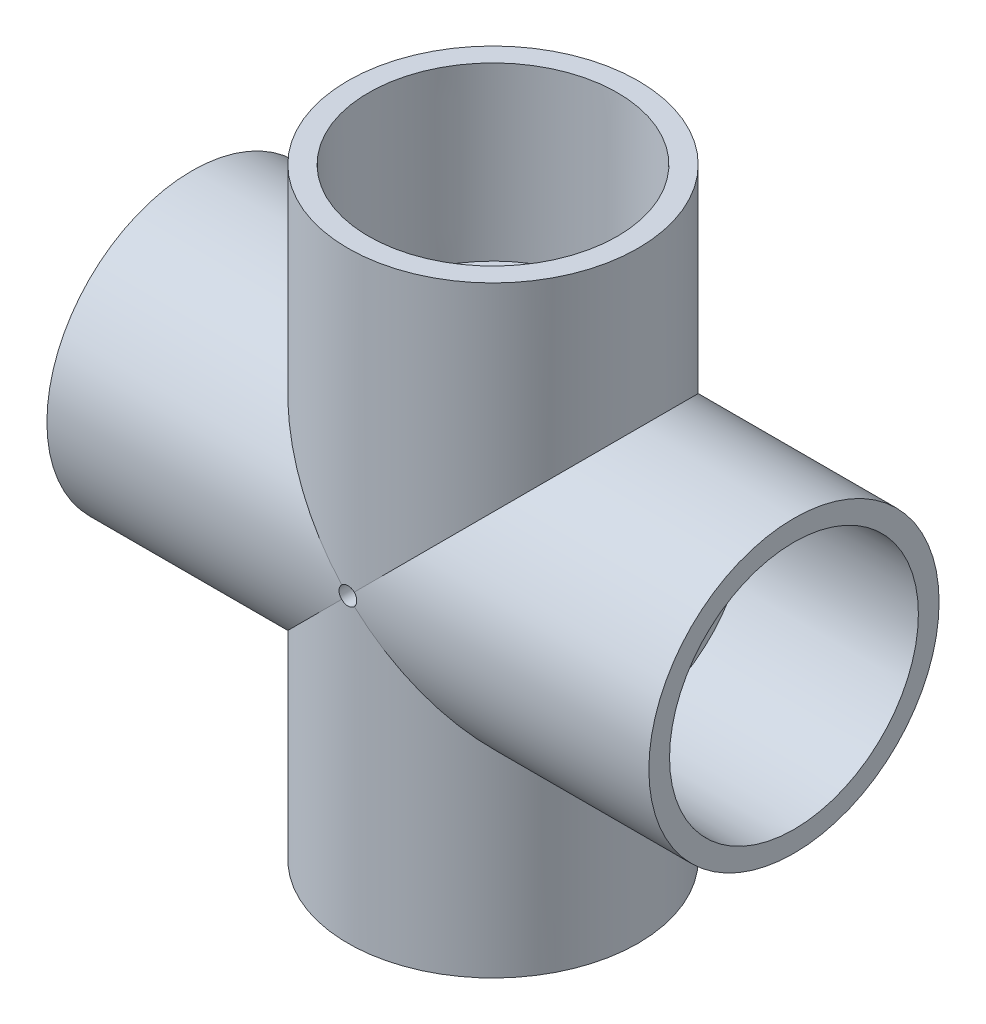
SolidWorks part; units mm, degrees
ref_plane "Front Plane" through (0, 0, 0) normal (0, 0, 1) x (1, 0, 0)
ref_plane "Top Plane" through (0, 0, 0) normal (0, 1, 0) x (1, 0, 0)
ref_plane "Right Plane" through (0, 0, 0) normal (1, 0, 0) x (0, 0, -1)
sketch "Sketch0" plane through (0, 0, 0) normal (0, 0, 1) x (1, 0, 0)
  line L0 (-58.7375, 0) -> (0, 0) construction
  line L1 (0, 0) -> (0, 58.7375) construction
  line L2 (-25.4, 0) -> (0, 0) construction
  line L3 (0, 0) -> (0, 25.4) construction
  line L4 (-58.7375, 28.321) -> (-58.7375, -28.321) construction
  line L5 (-25.4, 24.0538) -> (-58.7375, 24.2824) construction
  line L6 (-25.4, 24.0538) -> (-25.4, -24.0538) construction
  line L7 (-25.4, -24.0538) -> (-58.7375, -24.2824) construction
  line L8 (-58.7375, 24.2824) -> (-58.7375, -24.2824) construction
  line L9 (-28.321, 58.7375) -> (28.321, 58.7375) construction
  line L10 (-24.2824, 58.7375) -> (24.2824, 58.7375) construction
  line L11 (24.2824, 58.7375) -> (24.0538, 25.4) construction
  line L12 (24.0538, 25.4) -> (-24.0538, 25.4) construction
  line L13 (-24.0538, 25.4) -> (-24.2824, 58.7375) construction
  line L14 (-25.4, 20.447) -> (-25.4, -20.447) construction
  line L15 (-58.7375, 0) -> (-25.4, 0) construction
  line L16 (0, 58.7375) -> (0, 25.4) construction
  line L17 (0, 0) -> (25.4, 0) construction
  line L18 (-20.447, 25.4) -> (20.447, 25.4) construction
  line L19 (25.4, 0) -> (58.7375, 0) construction
  line L20 (0, 0) -> (0, -25.4) construction
  line L21 (0, -25.4) -> (0, -58.7375) construction
  dimension "H" = 58.7375
  dimension "G" = 25.4
  dimension "M" = 56.642
  dimension "OD A" = 48.5648
  dimension "OD B" = 48.1076
  dimension "ID" = 40.894
sketch "Sketch1" plane through (0, 0, 0) normal (0, 0, 1) x (1, 0, 0)
  line L0 (-58.7375, 0) -> (0, 0) construction
  line L1 (-58.7375, 0) -> (0, 0) construction
  line L2 (0, 0) -> (0, -28.321) construction
  line L3 (-58.7375, -28.321) -> (-25.4, -28.321)
  line L4 (-58.7375, -28.321) -> (-58.7375, -24.2824)
  line L5 (-58.7375, -24.2824) -> (-25.4, -24.0538)
  line L6 (-25.4, -28.321) -> (-25.4, -24.0538)
  line L7 (-25.4, -28.321) -> (0, -28.321) construction
  line L8 (58.7375, -24.2824) -> (25.4, -24.0538)
  line L9 (58.7375, -28.321) -> (58.7375, -24.2824)
  line L10 (25.4, -28.321) -> (25.4, -24.0538)
  line L11 (58.7375, -28.321) -> (25.4, -28.321)
revolve "Revolve1" add sketch "Sketch1" angle 360 about L1
sketch "Sketch2" plane through (0, 0, 0) normal (0, 0, 1) x (1, 0, 0)
  line L0 (24.2824, 58.7375) -> (24.0538, 25.4)
  line L1 (24.0538, 25.4) -> (28.321, 25.4)
  line L2 (28.321, 25.4) -> (28.321, 58.7375)
  line L3 (28.321, 58.7375) -> (24.2824, 58.7375)
  line L4 (0, 0) -> (0, 58.7375) construction
  line L5 (0, 0) -> (0, 58.7375) construction
  line L6 (0, 0) -> (25.4, 0) construction
  line L7 (28.321, -58.7375) -> (24.2824, -58.7375)
  line L8 (28.321, -25.4) -> (28.321, -58.7375)
  line L9 (24.0538, -25.4) -> (28.321, -25.4)
  line L10 (24.2824, -58.7375) -> (24.0538, -25.4)
revolve "Revolve2" add sketch "Sketch2" angle 360 about L5
sketch "Sketch3" plane through (-25.4, 0, 0) normal (1, 0, 0) x (0, 0, -1)
  circle A0 centre (0, 0) radius 20.447
  circle A1 centre (0, 0) radius 28.321
sketch "Sketch4" plane through (-25.4, 0, 0) normal (1, 0, 0) x (0, 0, -1)
  circle A0 centre (0, 0) radius 28.321 construction
  circle A1 centre (0, 0) radius 28.321
extrude "Boss-Extrude1" add sketch "Sketch4" along normal up to vertex
sketch "Sketch5" plane through (0, 25.4, 0) normal (0, -1, 0) x (1, 0, 0)
  circle A0 centre (0, 0) radius 28.321 construction
  circle A1 centre (0, 0) radius 28.321
extrude "Boss-Extrude2" add sketch "Sketch5" along normal up to vertex (50.8 mm away) up to point (0, -25.4, 0)
sketch "Sketch6" plane through (0, 0, 0) normal (0, 0, 1) x (1, 0, 0)
  line L0 (-58.7375, -24.2824) -> (-25.4, -24.0538)
  line L1 (-25.4, -24.0538) -> (-25.4, -20.447)
  line L2 (-25.4, -20.447) -> (25.4, -20.447)
  line L3 (25.4, -20.5345) -> (25.4, 20.5345) construction
  line L4 (0, -20.447) -> (0, 0) construction
  line L5 (25.4, -24.0538) -> (25.4, -20.447)
  line L6 (58.7375, -24.2824) -> (58.7375, 24.2824) construction
  line L7 (58.7375, -28.321) -> (58.7375, 28.321) construction
  line L8 (58.7375, -24.2824) -> (58.7375, 0)
  line L9 (58.7375, 0) -> (-58.7375, 0)
  line L10 (-58.7375, 0) -> (-58.7375, -24.2824)
  line L11 (58.7375, -24.2824) -> (25.4, -24.0538)
revolve "Cut-Revolve1" cut sketch "Sketch6" angle 360 about L9
sketch "Sketch7" plane through (0, 0, 0) normal (0, 0, 1) x (1, 0, 0)
  line L0 (24.2824, 58.7375) -> (24.0538, 25.4)
  line L1 (24.0538, 25.4) -> (20.447, 25.4)
  line L2 (20.447, 25.4) -> (20.447, -25.4)
  line L4 (20.447, 0) -> (0, 0) construction
  line L5 (0, 58.7375) -> (0, -58.7375)
  line L6 (-28.321, 58.7375) -> (28.321, 58.7375) construction
  line L7 (0, 58.7375) -> (24.2824, 58.7375)
  line L8 (24.0538, -25.4) -> (20.447, -25.4)
  line L9 (24.2824, -58.7375) -> (24.0538, -25.4)
  line L10 (0, 0) -> (25.4, 0) construction
  line L11 (0, -58.7375) -> (24.2824, -58.7375)
revolve "Cut-Revolve2" cut sketch "Sketch7" angle 360 about L5
hole_wizard "#8-36 Tapped Hole1" positions "Sketch9" profile "Sketch8" tap size "#8-36" standard "ANSI Inch"
sketch "Sketch9" plane through (0, 0, 0) normal (0, 0, 1) x (1, 0, 0)
  point P0 (0, 0)
sketch "Sketch8" plane through (0, 0, 0) normal (1, 0, 0) x (0, 1, 0)
  line L0 (0, 0) -> (0, 28.321)
  line L1 (0, 28.321) -> (1.7272, 28.321)
  line L2 (1.7272, 28.321) -> (1.7272, 0)
  line L5 (1.7272, 0) -> (0, 0)
  line L11 (0, -6.35) -> (0, 107.95) construction
  dimension "Thru Tap Drill Dia." = 3.4544
  dimension "Thru Tap Drill Depth" = 28.321
cosmetic thread "Hole Thread1" parameters "D2"=4.1656
